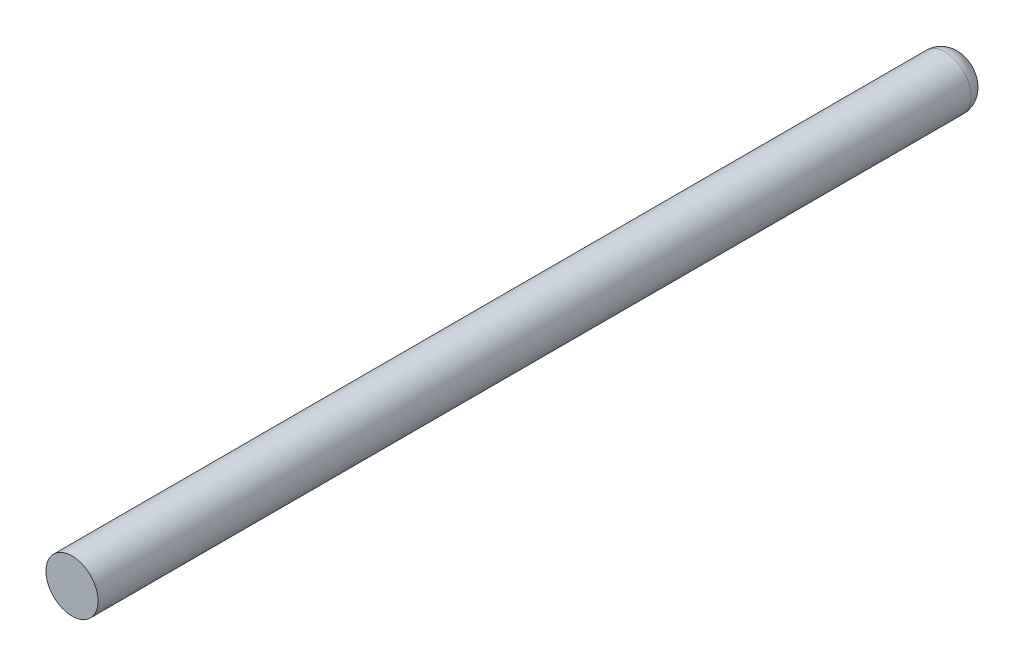
SolidWorks part; units mm, degrees
ref_plane "Front Plane" through (0, 0, 0) normal (0, 0, 1) x (1, 0, 0)
ref_plane "Top Plane" through (0, 0, 0) normal (0, 1, 0) x (1, 0, 0)
ref_plane "Right Plane" through (0, 0, 0) normal (1, 0, 0) x (0, 0, -1)
sketch "Sketch1" plane through (0, 0, 0) normal (0, 0, 1) x (1, 0, 0)
  circle A0 centre (0, 0) radius 3.9751
  dimension "D1" = 7.9502
extrude "Boss-Extrude1" add sketch "Sketch1" along normal blind 135.636
fillet "Fillet2" radius 2.54 1 edges at (3.9751, 0, 0)
